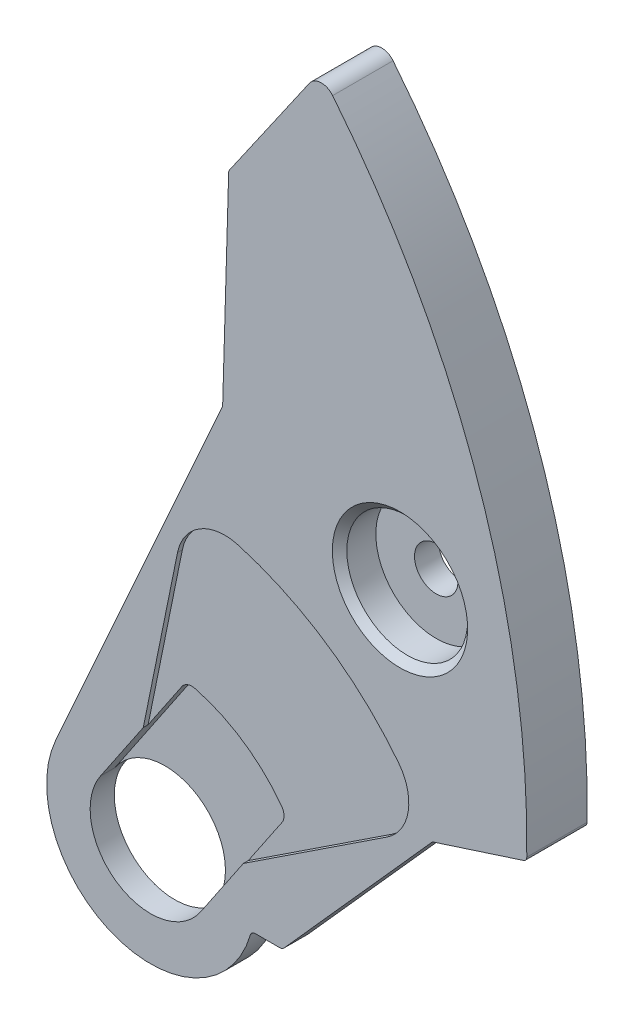
SolidWorks part; units mm, degrees
ref_plane "Alzado" through (0, 0, 0) normal (0, 0, 1) x (1, 0, 0)
ref_plane "Planta" through (0, 0, 0) normal (0, 1, 0) x (1, 0, 0)
ref_plane "Vista lateral" through (0, 0, 0) normal (1, 0, 0) x (0, 0, -1)
ref_plane "Plane1" through (0, 0, 0) normal (0, 0, -1) x (-1, 0, 0)
sketch "Sketch1" plane through (0, 0, 0) normal (0, 0, -1) x (-1, 0, 0)
  line L0 (-18.1472, -0.3211) -> (-16.6405, -0.8076)
  line L1 (-11.1231, 3.054) -> (-11.8548, 4.688)
  line L2 (-11.8548, 4.688) -> (-11.9801, 8.9661)
  line L3 (-11.9801, 8.9661) -> (-13.6512, 11.3729)
  arc A0 (-14.1312, 11.39) -> (-18.1472, -0.3211) centre (0, 0) ccw
  arc A1 (-16.6405, -0.8076) -> (-11.1231, 3.054) centre (-10.3629, -3.9046) cw
  arc A2 (-13.6512, 11.3729) -> (-14.1312, 11.39) centre (-13.8976, 11.2018) ccw
  dimension "D1" = 18.15
  dimension "D2" = 7
  dimension "D3" = 0.3
  dimension "D4" = 1.5067
  dimension "D5" = 4.016
  dimension "D6" = 18.1472
  dimension "D7" = 4.496
  dimension "D8" = 6.167
  dimension "D9" = 6.2924
  dimension "D10" = 7.0241
  dimension "D11" = 7.7843
  dimension "D12" = 3.5835
  dimension "D13" = 8.5926
extrude "Boss-Extrude1" add sketch "Sketch1" against normal blind 0.75
sketch "Sketch2" plane through (0, 0, 0.75) normal (0, 0, 1) x (1, 0, 0)
  line L0 (18.1472, -0.3211) -> (16.1969, -0.9508)
  line L1 (16.1969, -0.9508) -> (13.09, -4.428)
  line L2 (13.09, -4.428) -> (12.4482, -4.428)
  line L3 (8.4006, -3.0259) -> (11.8548, 4.688)
  line L4 (11.8548, 4.688) -> (11.9801, 8.9661)
  line L5 (11.9801, 8.9661) -> (13.6512, 11.3729)
  arc A0 (12.4482, -4.428) -> (8.4006, -3.0259) centre (10.3629, -3.9046) cw
  arc A1 (13.6512, 11.3729) -> (14.1312, 11.39) centre (13.8976, 11.2018) cw
  arc A2 (14.1312, 11.39) -> (18.1472, -0.3211) centre (0, 0) cw
  dimension "D1" = 2.15
  dimension "D2" = 0.3
  dimension "D3" = 18.15
  dimension "D4" = 2.0658
  dimension "D5" = 4.016
  dimension "D6" = 0.2336
  dimension "D7" = 0.48
  dimension "D8" = 1.0411
  dimension "D9" = 1.683
  dimension "D10" = 2.151
  dimension "D11" = 2.2764
  dimension "D12" = 3.7683
  dimension "D13" = 5.7306
  dimension "D14" = 6.7021
  dimension "D15" = 12.3408
extrude "Boss-Extrude2" add sketch "Sketch2" along normal blind 0.5
sketch "Sketch3" plane through (0, 0, 1.25) normal (0, 0, 1) x (1, 0, 0)
  line L0 (11.1188, 2.5714) -> (10.2128, -1.8938)
  line L1 (10.2128, -1.8938) -> (9.3271, -3.2049)
  line L2 (11.3986, -4.6043) -> (12.2844, -3.2932)
  line L3 (12.2844, -3.2932) -> (16.0887, -0.786)
  arc A0 (16.0887, -0.786) -> (11.1188, 2.5714) centre (10.3629, -3.9046) ccw
  arc A1 (9.3271, -3.2049) -> (11.3986, -4.6043) centre (10.3629, -3.9046) cw
  dimension "D1" = 6.52
  dimension "D2" = 1.25
  dimension "D3" = 0.9265
  dimension "D4" = 1.8122
  dimension "D5" = 1.9623
  dimension "D6" = 2.7182
  dimension "D7" = 2.998
  dimension "D8" = 3.8838
  dimension "D9" = 7.6881
  dimension "D10" = 1.1322
extrude "Cut-Extrude1" cut sketch "Sketch3" against normal blind 0.1
sketch "Sketch4" plane through (0, 0, 1.15) normal (0, 0, 1) x (1, 0, 0)
  line L0 (11.0065, -0.719) -> (9.3271, -3.2049)
  line L1 (11.3986, -4.6043) -> (13.078, -2.1185)
  arc A0 (9.3271, -3.2049) -> (11.3986, -4.6043) centre (10.3629, -3.9046) cw
  arc A1 (13.078, -2.1185) -> (11.0065, -0.719) centre (10.3629, -3.9046) ccw
  dimension "D1" = 1.25
  dimension "D2" = 3.25
  dimension "D3" = 1.0358
  dimension "D4" = 2.0716
extrude "Cut-Extrude2" cut sketch "Sketch4" against normal blind 0.2
ref_plane "Plane2" through (0, 0.612, 0) normal (0, 1, 0) x (1, 0, 0)
sketch "Sketch5" plane through (0, 0.612, 0) normal (0, 1, 0) x (1, 0, 0)
  line L0 (17.441, 0.6) -> (16.991, 0.6)
  line L1 (16.991, 0.6) -> (16.991, 0)
  line L2 (16.991, 0) -> (17.441, 0)
  line L3 (17.441, 0) -> (17.441, 0.6)
  line L4 (16.991, 0.6) -> (16.991, 0) construction
  dimension "D1" = 0.45
  dimension "D2" = 0.6
revolve "Revolve1" add sketch "Sketch5" angle 360 about L4
ref_plane "Plane3" through (0, 8.246, 0) normal (0, 1, 0) x (1, 0, 0)
sketch "Sketch6" plane through (0, 8.246, 0) normal (0, 1, 0) x (1, 0, 0)
  line L0 (14.7601, 0.6) -> (14.3101, 0.6)
  line L1 (14.3101, 0.6) -> (14.3101, 0)
  line L2 (14.3101, 0) -> (14.7601, 0)
  line L3 (14.7601, 0) -> (14.7601, 0.6)
  line L4 (14.3101, 0.6) -> (14.3101, 0) construction
  dimension "D1" = 0.45
  dimension "D2" = 0.6
revolve "Revolve2" add sketch "Sketch6" angle 360 about L4
ref_plane "Plane4" through (0, -3.9046, 0) normal (0, -1, 0) x (1, 0, 0)
sketch "Sketch7" plane through (0, -3.9046, 0) normal (0, -1, 0) x (1, 0, 0)
  line L0 (11.6129, 1.25) -> (10.3629, 1.25)
  line L1 (10.3629, 1.25) -> (10.3629, 0.75)
  line L2 (10.3629, 0.75) -> (11.6129, 0.75)
  line L3 (11.6129, 0.75) -> (11.6129, 1.25)
  line L4 (10.3629, 1.25) -> (10.3629, 0.75) construction
  dimension "D1" = 1.25
  dimension "D2" = 0.5
revolve "Cut-Revolve1" cut sketch "Sketch7" angle 360 about L4
hole_wizard "Hole1" positions "Sketch9" profile "Sketch8" legacy
sketch "Sketch9" plane through (0, 0, 1.25) normal (0, 0, 1) x (1, 0, 0)
  point P0 (15.5247, 3.2314)
sketch "Sketch8" plane through (15.5247, 3.2314, 1.25) normal (1, 0, 0) x (0, -1, 0)
  line L0 (0, 0) -> (0, 1.85)
  line L1 (0, 1.85) -> (0.45, 1.85)
  line L2 (0.45, 1.85) -> (0.45, 0.75)
  line L3 (0.45, 0.75) -> (1.25, 0.75)
  line L4 (1.25, 0.75) -> (1.25, 0)
  line L5 (1.25, 0) -> (0, 0)
  line L6 (0, 110) -> (0, -10) construction
  dimension "Diameter" = 0.9
  dimension "Depth" = 1.85
  dimension "C-Bore Diameter" = 2.5
  dimension "C-Bore Depth" = 0.75
fillet "Fillet1" radius 0.1 8 edges at (14.7601, 8.246, -0.6) (11.8548, 4.688, 0.625) (12.4482, -4.428, 1) (17.441, 0.612, -0.6) (11.9801, 8.9661, 0.625) (13.09, -4.428, 1) (18.1472, -0.3211, 0.625) (16.1969, -0.9508, 1)
chamfer "Chamfer1" distance 0.15 angle 45 1 edges at (16.7747, 3.2314, 1.25)
fillet "Fillet2" radius 0.25 2 edges at (13.078, -2.1185, 1.05) (11.0065, -0.719, 1.05)
fillet "Fillet3" radius 1 2 edges at (11.1188, 2.5714, 1.2) (16.0887, -0.786, 1.2)
